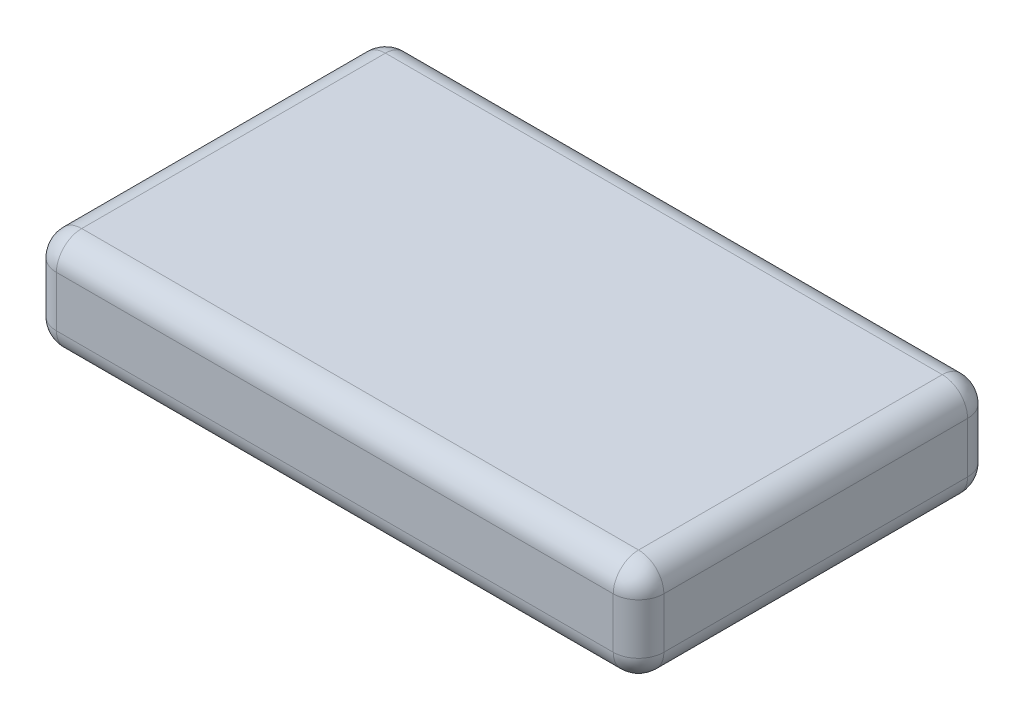
SolidWorks part; units mm, degrees
ref_plane "Front Plane" through (0, 0, 0) normal (0, 0, 1) x (1, 0, 0)
ref_plane "Top Plane" through (0, 0, 0) normal (0, 1, 0) x (1, 0, 0)
ref_plane "Right Plane" through (0, 0, 0) normal (1, 0, 0) x (0, 0, -1)
sketch "Sketch1" plane through (0, 0, 0) normal (0, 1, 0) x (1, 0, 0)
  line L0 (0, 0) -> (609.6, 0)
  line L1 (609.6, 0) -> (609.6, 355.6)
  line L2 (609.6, 355.6) -> (0, 355.6)
  line L3 (0, 355.6) -> (0, 0)
  dimension "D1" = 609.6
  dimension "D2" = 355.6
extrude "Boss-Extrude1" add sketch "Sketch1" along normal blind 101.6
fillet "Fillet1" radius 25.4 12 edges at (0, 101.6, -177.8) (0, 0, -177.8) (0, 50.8, -355.6) (304.8, 0, -355.6) (304.8, 101.6, -355.6) (609.6, 50.8, -355.6) (609.6, 0, -177.8) (609.6, 101.6, -177.8) (609.6, 50.8, 0) (0, 50.8, 0) (304.8, 0, 0) (304.8, 101.6, 0)
